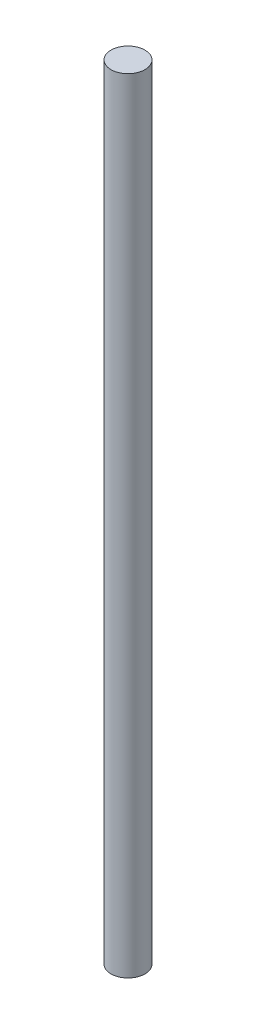
SolidWorks part; units mm, degrees
ref_plane "Front Plane" through (0, 0, 0) normal (0, 0, 1) x (1, 0, 0)
ref_plane "Top Plane" through (0, 0, 0) normal (0, 1, 0) x (1, 0, 0)
ref_plane "Right Plane" through (0, 0, 0) normal (1, 0, 0) x (0, 0, -1)
sketch "Sketch1" plane through (0, 0, 0) normal (0, 1, 0) x (1, 0, 0)
  circle A0 centre (0, 0) radius 1.3
  dimension "D1" = 2.6
extrude "Boss-Extrude1" add sketch "Sketch1" along normal blind 60
